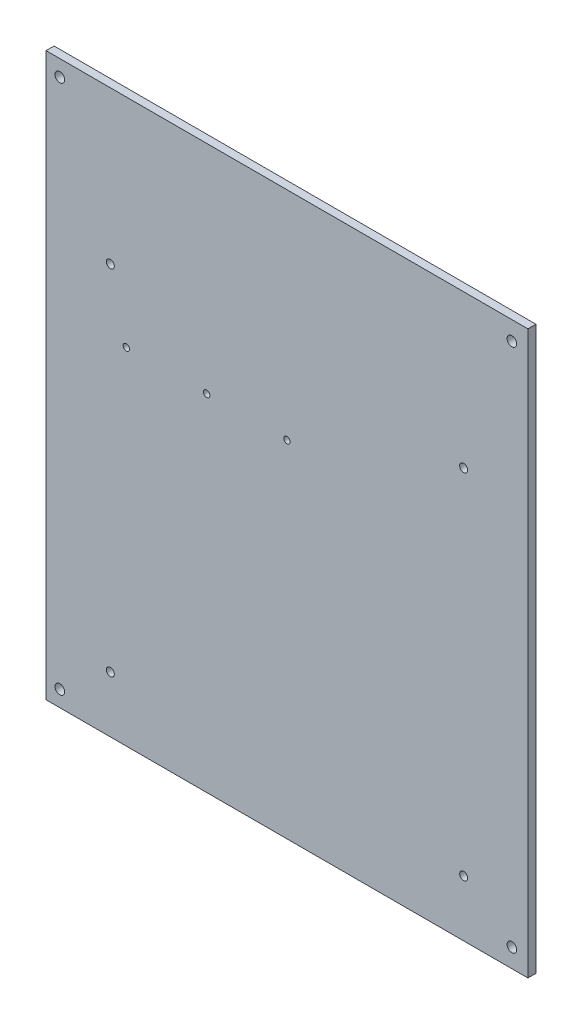
SolidWorks part; units mm, degrees
material "ABS"
ref_plane "Front Plane" through (0, 0, 0) normal (0, 0, 1) x (1, 0, 0)
ref_plane "Top Plane" through (0, 0, 0) normal (0, 1, 0) x (1, 0, 0)
ref_plane "Right Plane" through (0, 0, 0) normal (1, 0, 0) x (0, 0, -1)
sketch "Sketch1" plane through (0, 0, 0) normal (0, 0, 1) x (1, 0, 0)
  line L0 (-150, 0) -> (150, 0) construction
  line L1 (-150, 175) -> (150, 175)
  line L2 (-150, 175) -> (-150, -175)
  line L3 (-150, -175) -> (150, -175)
  line L4 (150, 175) -> (150, -175)
  line L5 (-150, 175) -> (150, -175) construction
  line L6 (-150, -175) -> (150, 175) construction
  circle A0 centre (-141.4286, 165) radius 3
  circle A1 centre (140, 163.3333) radius 3
  circle A2 centre (140, -163.3333) radius 3
  circle A3 centre (-141.4286, -165) radius 3
  point P0 (0, 0)
  dimension "D2" = 6
  dimension "D1" = 300
  dimension "D3" = 10
  dimension "D4" = 10
  dimension "D5" = 350
extrude "Boss-Extrude1" add sketch "Sketch1" along normal blind 5
sketch "Sketch2" plane through (0, 0, 0) normal (0, 0, -1) x (-1, 0, 0)
  line L0 (150, -175) -> (-150, -175) construction
  line L1 (110, -140) -> (-110, -140) construction
  line L2 (110, -140) -> (110, 80) construction
  line L3 (110, 80) -> (-110, 80) construction
  line L4 (-110, -140) -> (-110, 80) construction
  line L5 (110, -30) -> (-110, -30) construction
  circle A4 centre (110, -140) radius 2.5
  circle A5 centre (-110, -140) radius 2.5
  circle A6 centre (-110, 80) radius 2.5
  circle A7 centre (110, 80) radius 2.5
  point P0 (0, 0)
  point P16 (0, 0)
  dimension "D2" = 5
  dimension "D1" = 220
  dimension "D4" = 35
  dimension "D3" = 2
extrude "Cut-Extrude1" cut sketch "Sketch2" against normal blind 10
sketch "Sketch3" plane through (0, 0, 0) normal (0, 0, -1) x (-1, 0, 0)
  line L0 (0, -175) -> (0, 40) construction
  line L1 (150, -175) -> (-150, -175) construction
  line L2 (-150, 40) -> (150, 40) construction
  line L3 (150, 175) -> (150, -175) construction
  circle A0 centre (0, 40) radius 2
  circle A1 centre (50, 40) radius 2
  circle A2 centre (100, 40) radius 2
  point P10 (0, 40)
  dimension "D2" = 4
  dimension "D1" = 215
  dimension "D3" = 3
extrude "Cut-Extrude2" cut sketch "Sketch3" against normal through all
